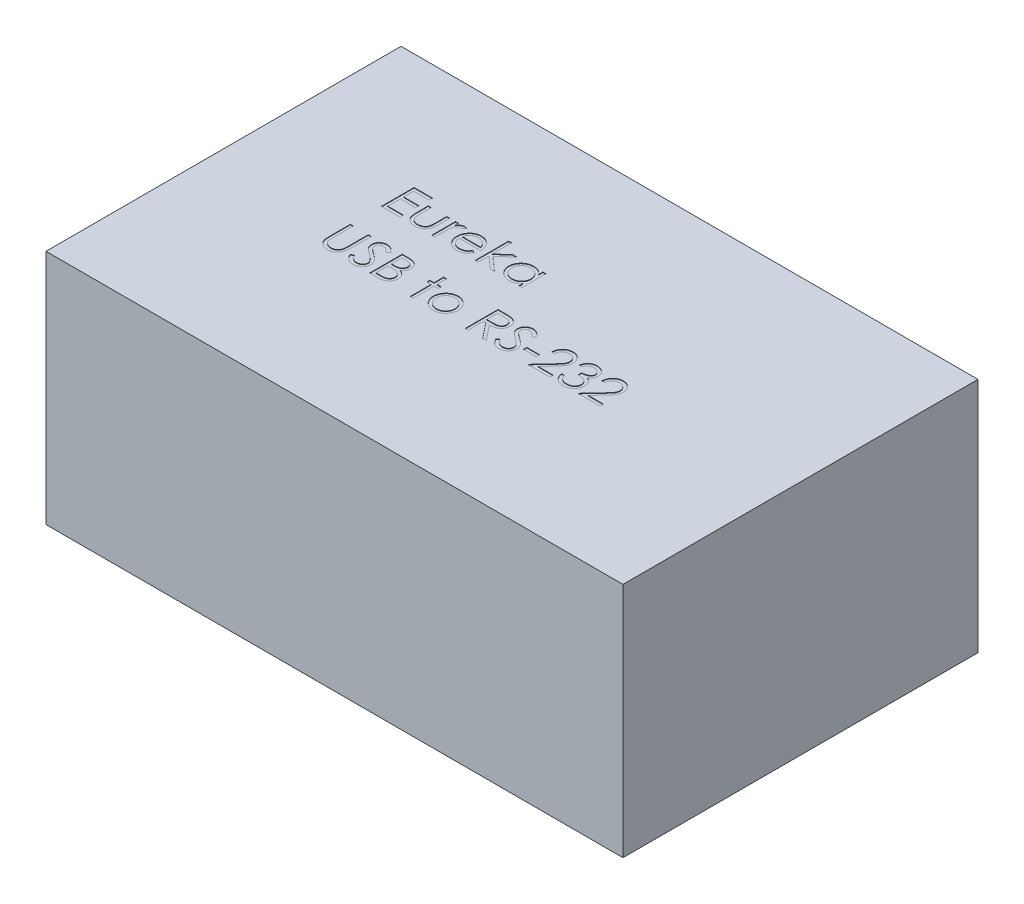
SolidWorks part; units mm, degrees
ref_plane "Front Plane" through (0, 0, 0) normal (0, 0, 1) x (1, 0, 0)
ref_plane "Top Plane" through (0, 0, 0) normal (0, 1, 0) x (1, 0, 0)
ref_plane "Right Plane" through (0, 0, 0) normal (1, 0, 0) x (0, 0, -1)
sketch "Sketch1" plane through (0, 0, 0) normal (0, 1, 0) x (1, 0, 0)
  line L1 (30.9563, 19.05) -> (-30.9562, 19.05)
  line L2 (30.9563, 19.05) -> (30.9563, -19.05)
  line L3 (30.9563, -19.05) -> (-30.9562, -19.05)
  line L4 (-30.9562, 19.05) -> (-30.9562, -19.05)
  line L5 (30.9563, 19.05) -> (-30.9562, -19.05) construction
  line L6 (30.9563, -19.05) -> (-30.9562, 19.05) construction
  point P0 (0, 0)
  dimension "D1" = 38.1
  dimension "D2" = 61.9125
extrude "Boss-Extrude1" add sketch "Sketch1" along normal blind 25.4
sketch "Sketch2" plane through (0, 25.4, 0) normal (0, 1, 0) x (1, 0, 0)
  text T0 "Eureka\r\nUSB to RS-232"
extrude "Cut-Extrude1" cut sketch "Sketch2" against normal blind 0.05
